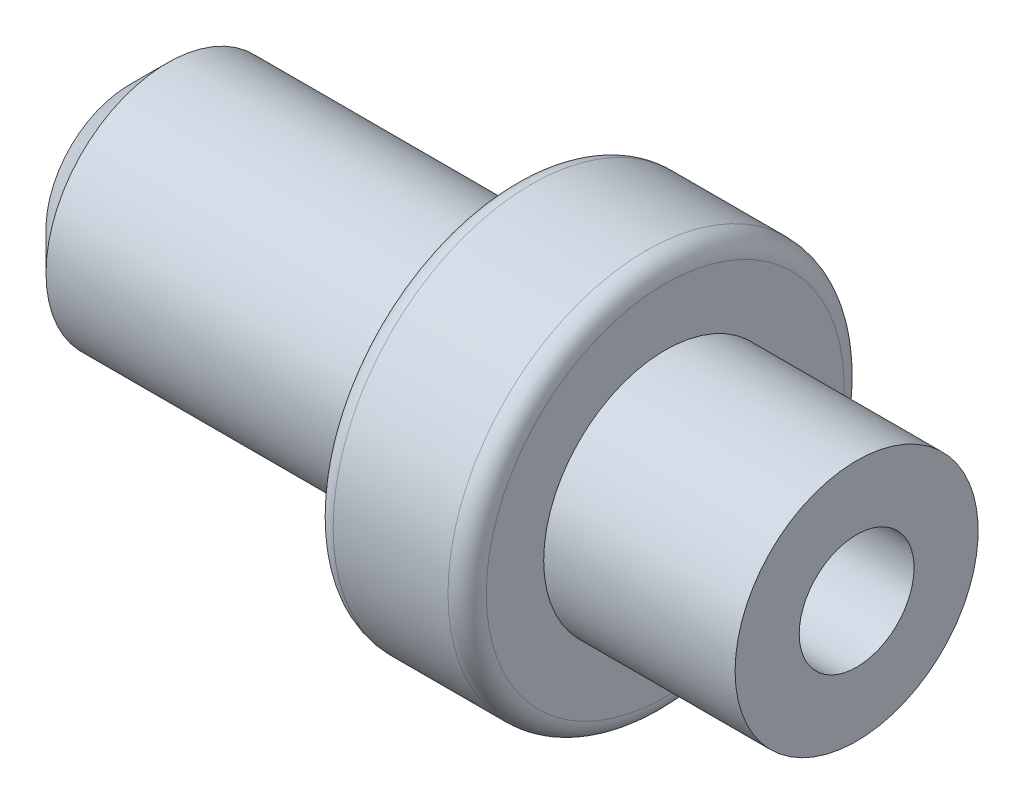
SolidWorks part; units mm, degrees
ref_plane "Front Plane" through (0, 0, 0) normal (0, 0, 1) x (1, 0, 0)
ref_plane "Top Plane" through (0, 0, 0) normal (0, 1, 0) x (1, 0, 0)
ref_plane "Right Plane" through (0, 0, 0) normal (1, 0, 0) x (0, 0, -1)
sketch "Sketch1" plane through (0, 0, 0) normal (0, 0, 1) x (1, 0, 0)
  line L0 (-34.8244, 0) -> (44.2505, 0) construction
  line L1 (-10, 1.5) -> (-10, 3.175)
  line L2 (-10, 3.175) -> (0, 3.175)
  line L3 (0, 3.175) -> (0, 5.175)
  line L4 (0, 5.175) -> (4, 5.175)
  line L5 (4, 5.175) -> (4, 3.175)
  line L6 (4, 3.175) -> (9, 3.175)
  line L7 (9, 3.175) -> (9, 1.5)
  line L8 (9, 1.5) -> (-10, 1.5)
  dimension "D1" = 3
  dimension "D2" = 6.35
  dimension "D3" = 2
  dimension "D4" = 2
  dimension "D5" = 10
  dimension "D6" = 5
  dimension "D7" = 4
revolve "Revolve1" add sketch "Sketch1" angle 360 about L0
chamfer "Chamfer1" distance 1 angle 45 1 edges at (-10, 0, 3.175)
fillet "Fillet1" radius 0.5 2 edges at (4, 0, 5.175) (0, 0, 5.175)
